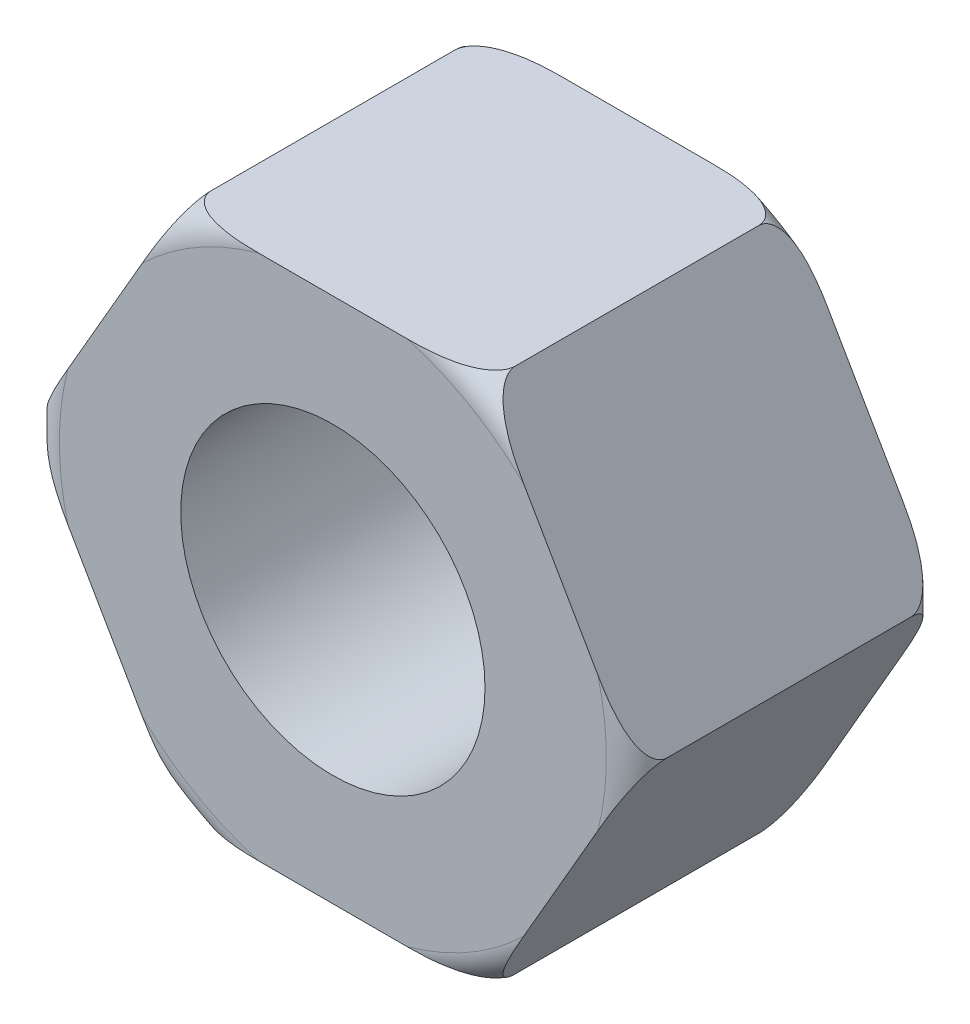
SolidWorks part; units mm, degrees
ref_plane "Front Plane" through (0, 0, 0) normal (0, 0, 1) x (1, 0, 0)
ref_plane "Top Plane" through (0, 0, 0) normal (0, 1, 0) x (1, 0, 0)
ref_plane "Right Plane" through (0, 0, 0) normal (1, 0, 0) x (0, 0, -1)
sketch "Sketch1" plane through (0, 0, 0) normal (0, 0, 1) x (1, 0, 0)
  line L1 (-19.9763, 0) -> (-9.9882, -17.3)
  line L2 (-9.9882, -17.3) -> (9.9882, -17.3)
  line L3 (9.9882, -17.3) -> (19.9763, 0)
  line L4 (19.9763, 0) -> (9.9882, 17.3)
  line L5 (9.9882, 17.3) -> (-9.9882, 17.3)
  line L6 (-9.9882, 17.3) -> (-19.9763, 0)
  circle A0 centre (0, 0) radius 17.3 construction
  point P1 (0, 0)
  dimension "D1" = 34.6
extrude "Boss-Extrude1" add sketch "Sketch1" along normal blind 20
sketch "Sketch2" plane through (0, 0, 20) normal (0, 0, 1) x (1, 0, 0)
  circle A0 centre (0, 0) radius 10
  dimension "D1" = 20
extrude "Cut-Extrude1" cut sketch "Sketch2" against normal blind 20
sketch "Sketch3" plane through (0, 0, 0) normal (0, 1, 0) x (1, 0, 0)
  line L0 (19.9763, 0) -> (9.9882, 0) construction
  line L1 (19.9763, -20) -> (19.9763, 0) construction
  line L2 (19.9763, -2) -> (19.9763, 0)
  line L3 (19.9763, 0) -> (17.9763, 0)
  arc A0 (17.9763, 0) -> (19.9763, -2) centre (17.9763, -2) cw
  dimension "D1" = 2
revolve "Cut-Revolve1" cut sketch "Sketch3" angle 360 about axis through (0, 0, 0) along (0, 0, 1)
ref_plane "Plane1" through (0, 0, 10) normal (0, 0, -1) x (-1, 0, 0)
mirror "Mirror1" about plane through (0, 0, 10) normal (0, 0, -1) of "Cut-Revolve1"
